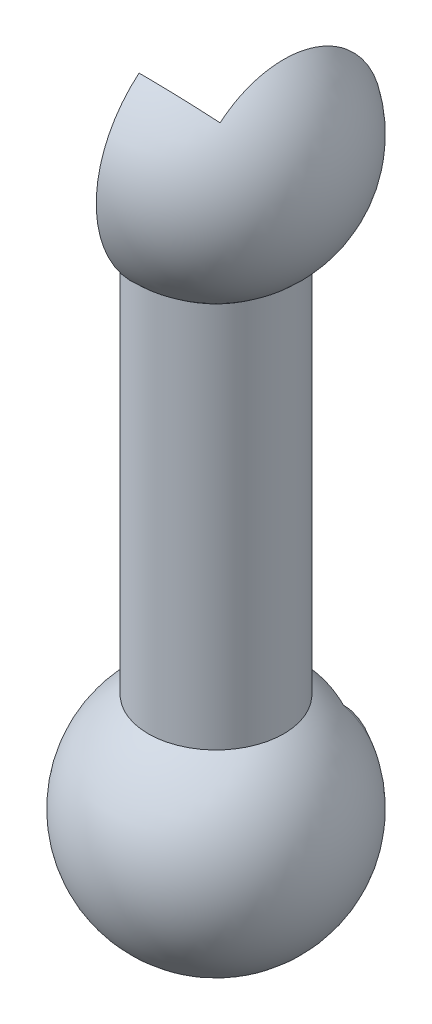
SolidWorks part; units mm, degrees
ref_plane "前视基准面" through (0, 0, 0) normal (0, 0, 1) x (1, 0, 0)
ref_plane "上视基准面" through (0, 0, 0) normal (0, 1, 0) x (1, 0, 0)
ref_plane "右视基准面" through (0, 0, 0) normal (1, 0, 0) x (0, 0, -1)
sketch "草图7" plane through (0, 0, 0) normal (0, 1, 0) x (1, 0, 0)
  line L14 (7.0315, 8.4457) -> (18.3717, 19.7859)
  line L38 (8.4457, 7.0315) -> (19.7859, 18.3717)
  line L57 (7.0315, -8.4457) -> (18.3717, -19.7859)
  line L58 (8.4457, -7.0315) -> (19.7859, -18.3717)
  line L61 (-8.4457, -7.0315) -> (-19.7859, -18.3717)
  line L62 (-7.0315, -8.4457) -> (-18.3717, -19.7859)
  line L65 (-8.4457, 7.0315) -> (-19.7859, 18.3717)
  line L66 (-7.0315, 8.4457) -> (-18.3717, 19.7859)
  line L68 (5, 5) -> (-5, -5) construction
  line L69 (-5, 5) -> (5, -5) construction
  line L70 (-5, 5) -> (5, 5) construction
  line L71 (1.127, 4) -> (-1.127, 4)
  line L73 (1.127, 6) -> (-1.127, 6)
  line L75 (1.127, 4) -> (-1.127, 6) construction
  line L76 (1.127, 6) -> (-1.127, 4) construction
  line L78 (4, -1.127) -> (4, 1.127)
  line L80 (6, -1.127) -> (6, 1.127)
  line L82 (-1.127, -4) -> (1.127, -4)
  line L84 (-1.127, -6) -> (1.127, -6)
  line L86 (-4, 1.127) -> (-4, -1.127)
  line L88 (-6, 1.127) -> (-6, -1.127)
  circle A1 centre (5, 5) radius 2
  circle A6 centre (0, 0) radius 30
  arc A7 (-19.7859, 18.3717) -> (-19.7859, -18.3717) centre (0, 0) ccw
  arc A8 (18.3717, 19.7859) -> (-18.3717, 19.7859) centre (0, 0) ccw
  arc A9 (19.7859, -18.3717) -> (19.7859, 18.3717) centre (0, 0) ccw
  circle A10 centre (5, -5) radius 2
  circle A11 centre (-5, -5) radius 2
  circle A12 centre (-5, 5) radius 2
  arc A13 (7.0315, 8.4457) -> (1.127, 6) centre (5, 5) ccw
  arc A14 (8.4457, -7.0315) -> (6, -1.127) centre (5, -5) ccw
  arc A15 (-7.0315, -8.4457) -> (-1.127, -6) centre (-5, -5) ccw
  arc A16 (-8.4457, 7.0315) -> (-6, 1.127) centre (-5, 5) ccw
  arc A17 (-18.3717, -19.7859) -> (18.3717, -19.7859) centre (0, 0) ccw
  arc A18 (-4, 1.127) -> (-1.127, 4) centre (-5, 5) ccw
  arc A19 (-6, -1.127) -> (-8.4457, -7.0315) centre (-5, -5) ccw
  arc A20 (4, -1.127) -> (1.127, -4) centre (5, -5) ccw
  arc A21 (6, 1.127) -> (8.4457, 7.0315) centre (5, 5) ccw
  arc A22 (-1.127, 6) -> (-7.0315, 8.4457) centre (-5, 5) ccw
  arc A23 (1.127, 4) -> (4, 1.127) centre (5, 5) ccw
  arc A24 (-1.127, -4) -> (-4, -1.127) centre (-5, -5) ccw
  arc A25 (1.127, -6) -> (7.0315, -8.4457) centre (5, -5) ccw
  point P0 (0, 0)
  point P2 (0, 5)
  point P21 (0, 0)
  point P22 (0, 0)
  point P34 (0, 0)
  point P47 (0, 0)
  point P60 (0, 0)
  dimension "D3" = 4
  dimension "D6" = 2
  dimension "D2" = 60
  dimension "D7" = 54
  dimension "D14" = 8
  dimension "D5" = 2
  dimension "D8" = 2
  dimension "D9" = 2
  dimension "D10" = 2
  dimension "D11" = 10
  dimension "D12" = 5
  dimension "D13" = 5
  dimension "D15" = 4
  dimension "D16" = 4
  dimension "D4" = 4
extrude "凸台-拉伸1" add sketch "草图7" along normal blind 178.35
sketch "草图8" plane through (0, 0, 0) normal (1, 0, 0) x (0, 0, -1)
  line L0 (30, 0) -> (30, 178.35) construction
  line L4 (0, 271.35) -> (0, 268.35)
  line L7 (0, 218.35) -> (0, 182.6378) construction
  line L8 (30, 178.35) -> (30, 174.6579)
  line L10 (30, 178.35) -> (-30, 178.35) construction
  line L11 (-23.7985, 218.35) -> (25.5416, 218.35) construction
  arc A4 (30, 174.6579) -> (0, 271.35) centre (0, 218.35) ccw
  arc A5 (30, 178.35) -> (0, 268.35) centre (0, 218.35) ccw
  dimension "D1" = 53
  dimension "D2" = 30
  dimension "D4" = 40
revolve "旋转1" add sketch "草图8" angle 180 about L7
sketch "草图14" plane through (0, 0, 0) normal (1, 0, 0) x (0, 0, -1)
  line L0 (0, 0) -> (0, -80) construction
  line L1 (-83.9634, -40) -> (83.9634, -40) construction
  line L3 (30, 3.6921) -> (30, 0)
  line L4 (30, 0) -> (30, 178.35) construction
  line L5 (0, -90) -> (0, -93)
  line L7 (-30, 0) -> (30, 0) construction
  arc A0 (0, -93) -> (30, 3.6921) centre (0, -40) ccw
  arc A1 (0, -90) -> (30, 0) centre (0, -40) ccw
  point P11 (0, -40)
  point P12 (0, -40)
  dimension "D1" = 106
  dimension "D2" = 100
  dimension "D3" = 40
revolve "旋转3" add sketch "草图14" angle 360 about L0
sketch "草图12" plane through (0, 0, 0) normal (0, 0, 1) x (1, 0, 0)
  line L0 (-30.1315, 218.35) -> (27.988, 218.35)
  line L1 (18.3717, 178.35) -> (-18.3717, 178.35) construction
  line L2 (-74.3943, -40) -> (106.8465, -40)
  line L4 (-30, 0) -> (30, 0) construction
  dimension "D1" = 40
  dimension "D2" = 40
ref_plane "基准面2" through (0, 218.35, 0) normal (0, 1, 0) x (1, 0, 0)
ref_plane "基准面3" through (0, -40, 0) normal (0, 1, 0) x (1, 0, 0)
sketch "草图13" plane through (0, 218.35, 0) normal (0, 1, 0) x (1, 0, 0)
  line L0 (-30.1315, 0) -> (27.988, 0) construction
  line L1 (29.9283, 32) -> (-32.0717, 32)
  line L2 (29.9283, 32) -> (29.9283, 95.4289)
  line L3 (29.9283, 95.4289) -> (-32.0717, 95.4289)
  line L4 (-32.0717, 32) -> (-32.0717, 95.4289)
  line L5 (-1.0717, 0) -> (-1.0717, 15.2558) construction
  dimension "D1" = 32
  dimension "D2" = 62
revolve "旋转2" add sketch "草图13" angle 130 about L0
sketch "草图15" plane through (0, -40, 0) normal (0, 1, 0) x (1, 0, 0)
  line L0 (0, 40.6136) -> (0, -22.8345) construction
  line L1 (22.5, 0) -> (-22.5, 0)
  line L2 (22.5, 0) -> (22.5, 69.2451)
  line L3 (22.5, 69.2451) -> (-22.5, 69.2451)
  line L4 (-22.5, 0) -> (-22.5, 69.2451)
  line L5 (22.5, 0) -> (-22.5, 69.2451) construction
  line L6 (22.5, 69.2451) -> (-22.5, 0) construction
  line L7 (-74.3943, 0) -> (106.8465, 0) construction
  point P0 (0, 34.6225)
  dimension "D1" = 45
revolve "旋转6" add sketch "草图15" angle 45 about L2
combine bodies "组合1" operation type subtract main body 135 bodies to subtract 137
combine bodies "组合2" operation type subtract main body 139 bodies to subtract 140
sketch "折弯-线1" plane through (0, 0, 0) normal (0, 1, 0) x (1, 0, 0)
sketch "边界框1" plane through (0, 0, 0) normal (0, 1, 0) x (1, 0, 0)
